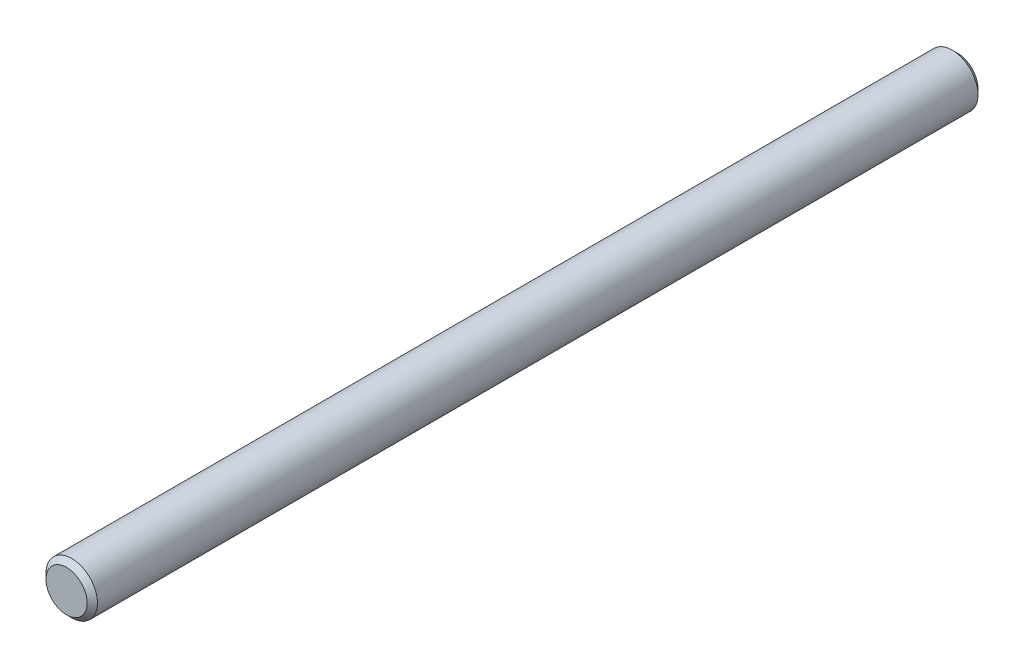
SolidWorks part; units mm, degrees
ref_plane "Front" through (0, 0, 0) normal (0, 0, 1) x (1, 0, 0)
ref_plane "Top" through (0, 0, 0) normal (0, 1, 0) x (1, 0, 0)
ref_plane "Right" through (0, 0, 0) normal (1, 0, 0) x (0, 0, -1)
sketch "Sketch1" plane through (0, 0, 0) normal (0, 0, 1) x (1, 0, 0)
  circle A0 centre (0, 0) radius 6.35
  dimension "dia" = 12.7
extrude "Extrude1" add sketch "Sketch1" along normal mid plane 220
sketch "Sketch2" plane through (0, 0, 0) normal (1, 0, 0) x (0, 0, -1)
  line L0 (110, 6.35) -> (88, 6.35) construction
  line L1 (110, 6.35) -> (-110, 6.35) construction
  line L2 (88, 6.35) -> (88, -6.35) construction
  line L3 (-110, -6.35) -> (110, -6.35) construction
  line L4 (100, 6.35) -> (100, -6.35) construction
  line L5 (-110, -6.35) -> (110, -6.35) construction
  point P0 (-110, 6.35)
  point P1 (110, 6.35)
  point P15 (100, 0)
  point P16 (88, 0)
  dimension "D1" = 22
  dimension "D2" = 12
chamfer "Chamfer1" distance 1.27 angle 45 2 edges at (6.35, 0, -110) (6.35, 0, 110)
sketch "Sketch3" plane through (0, 0, 110) normal (0, 0, 1) x (1, 0, 0)
  line L0 (0, -5.08) -> (0, 5.08) construction
  circle A0 centre (0, 0) radius 5.08 construction
equation "\"D1@Chamfer1\" = \"dia@Sketch1\" * .1"
